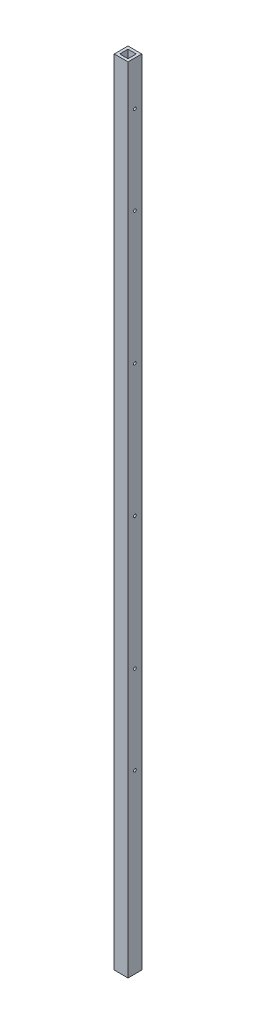
SolidWorks part; units mm, degrees
material "Polyethylene Cross-Linked"
ref_plane "Front Plane" through (0, 0, 0) normal (0, 0, 1) x (1, 0, 0)
ref_plane "Top Plane" through (0, 0, 0) normal (0, 1, 0) x (1, 0, 0)
ref_plane "Right Plane" through (0, 0, 0) normal (1, 0, 0) x (0, 0, -1)
sketch "Sketch1" plane through (0, 0, 0) normal (0, 1, 0) x (1, 0, 0)
  line L1 (0, 0) -> (31.75, 0)
  line L2 (0, 0) -> (0, 31.75)
  line L3 (0, 31.75) -> (31.75, 31.75)
  line L4 (31.75, 0) -> (31.75, 31.75)
  dimension "D1" = 31.75
  dimension "D2" = 31.75
extrude "Boss-Extrude1" add sketch "Sketch1" along normal blind 1828.8
sketch "Sketch2" plane through (0, 1828.8, 0) normal (0, 1, 0) x (1, 0, 0)
  line L1 (6.35, 6.35) -> (25.4, 6.35)
  line L2 (6.35, 6.35) -> (6.35, 25.4)
  line L3 (6.35, 25.4) -> (25.4, 25.4)
  line L4 (25.4, 6.35) -> (25.4, 25.4)
  line L5 (0, 0) -> (31.75, 0) construction
  line L6 (31.75, 0) -> (31.75, 31.75) construction
  dimension "D1" = 19.05
  dimension "D2" = 19.05
  dimension "D3" = 6.35
  dimension "D4" = 6.35
extrude "Cut-Extrude1" cut sketch "Sketch2" against normal through all
sketch "Sketch3" plane through (31.75, 0, 0) normal (1, 0, 0) x (0, 0, -1)
  line L0 (0, 1828.8) -> (0, 0) construction
  line L1 (0, 1828.8) -> (31.75, 1828.8) construction
  circle A0 centre (15.875, 1727.2) radius 3.175
  dimension "D1" = 6.35
  dimension "D2" = 15.875
  dimension "D3" = 101.6
extrude "Cut-Extrude2" cut sketch "Sketch3" against normal through all contours A0
sketch "Sketch4" plane through (31.75, 0, 0) normal (1, 0, 0) x (0, 0, -1)
  line L0 (0, 1828.8) -> (0, 0) construction
  line L1 (0, 1828.8) -> (31.75, 1828.8) construction
  line L2 (0, 0) -> (31.75, 0) construction
  circle A0 centre (15.875, 1524) radius 3.175
  circle A1 centre (15.875, 1219.2) radius 3.175
  circle A2 centre (15.875, 914.4) radius 3.175
  circle A3 centre (15.875, 609.6) radius 3.175
  circle A4 centre (15.875, 406.4) radius 3.175
  dimension "D1" = 6.35
  dimension "D4" = 6.35
  dimension "D5" = 609.6
  dimension "D6" = 6.35
  dimension "D7" = 914.4
  dimension "D8" = 6.35
  dimension "D10" = 6.35
  dimension "D2" = 15.875
  dimension "D3" = 304.8
  dimension "D9" = 609.6
  dimension "D11" = 406.4
extrude "Cut-Extrude3" cut sketch "Sketch4" against normal through all
